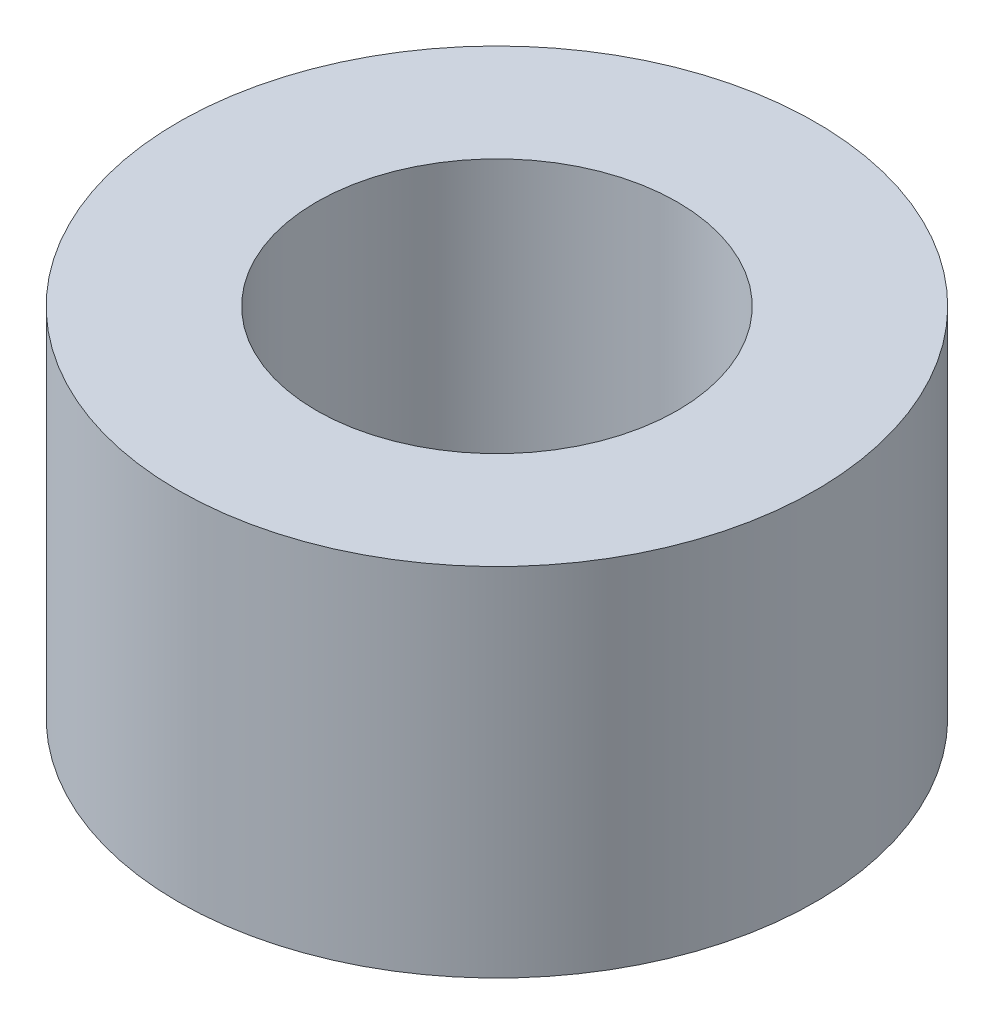
SolidWorks part; units mm, degrees
ref_plane "Front Plane" through (0, 0, 0) normal (0, 0, 1) x (1, 0, 0)
ref_plane "Top Plane" through (0, 0, 0) normal (0, 1, 0) x (1, 0, 0)
ref_plane "Right Plane" through (0, 0, 0) normal (1, 0, 0) x (0, 0, -1)
sketch "Sketch1" plane through (0, 0, 0) normal (0, 1, 0) x (1, 0, 0)
  circle A0 centre (0, 0) radius 3.2168
  circle A1 centre (0, 0) radius 5.6793
extrude "Boss-Extrude1" add sketch "Sketch1" along normal blind 6.35 contours A0 | A1
